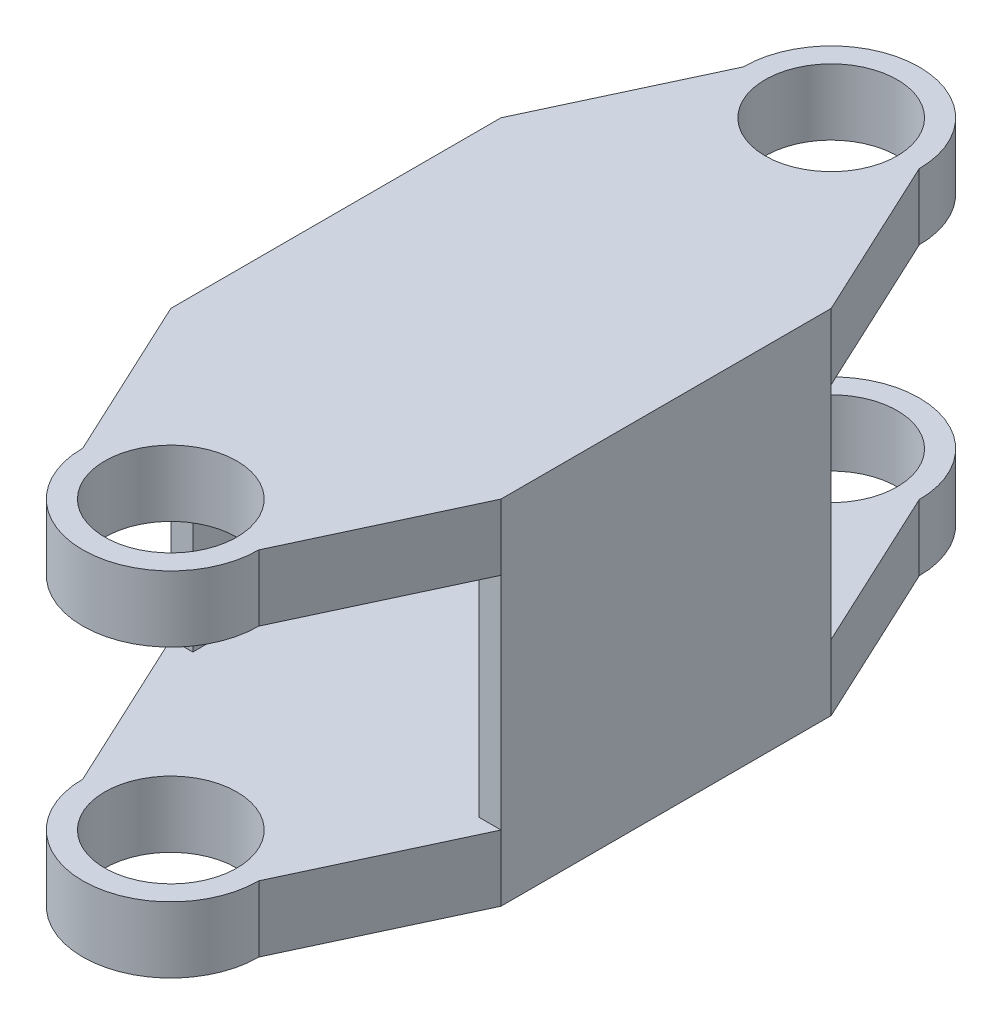
SolidWorks part; units mm, degrees
ref_plane "Plano frontal" through (0, 0, 0) normal (0, 0, 1) x (1, 0, 0)
ref_plane "Plano superior" through (0, 0, 0) normal (0, 1, 0) x (1, 0, 0)
ref_plane "Plano direito" through (0, 0, 0) normal (1, 0, 0) x (0, 0, -1)
ref_plane "Plane1" through (0, 5.01, 0) normal (0, 1, 0) x (1, 0, 0)
sketch "Sketch1" plane through (0, 5.01, 0) normal (0, 1, 0) x (1, 0, 0)
  line L0 (0, 19) -> (0, -11.6822) construction
  line L1 (14.8327, 0) -> (-20.4647, 0) construction
  line L2 (22.7509, 7.5) -> (-22.4164, 7.5) construction
  line L4 (-7.5, -7.5) -> (-7.5, 7.5)
  line L6 (7.5, -7.5) -> (7.5, 7.5)
  line L7 (-7.5, -7.5) -> (7.5, 7.5) construction
  line L8 (-7.5, 7.5) -> (7.5, -7.5) construction
  line L9 (-4, 15) -> (4, 15) construction
  line L10 (-4, 15) -> (-7.5, 7.5)
  line L11 (4, 15) -> (7.5, 7.5)
  line L12 (4, -15) -> (7.5, -7.5)
  line L13 (-4, -15) -> (-7.5, -7.5)
  arc A0 (-4, 15) -> (4, 15) centre (0, 15) cw
  circle A1 centre (0, 15) radius 3
  circle A2 centre (0, -15) radius 3
  arc A3 (-4, -15) -> (4, -15) centre (0, -15) ccw
  point P5 (0, 0)
  dimension "D5" = 6
  dimension "D1" = 15
  dimension "D2" = 8
  dimension "D3" = 4
  dimension "D4" = 7.5
extrude "Boss-Extrude1" add sketch "Sketch1" along normal blind 3
sketch "Sketch4" plane through (0, 5.01, 0) normal (0, 1, 0) x (1, 0, 0)
  line L0 (7.5, 7.5) -> (7.5, -7.5)
  line L1 (7.5, 7.5) -> (6.5, 7.5)
  line L2 (7.5, -7.5) -> (6.5, -7.5)
  line L3 (6.5, 7.5) -> (6.5, -7.5)
  dimension "D1" = 1
sketch "Sketch5" plane through (0, 0, 0) normal (0, 1, 0) x (1, 0, 0)
  line L0 (7.5, 7.5) -> (7.5, -7.5)
  line L1 (7.5, 7.5) -> (6.5, 7.5)
  line L2 (7.5, -7.5) -> (6.5, -7.5)
  line L3 (6.5, 7.5) -> (6.5, -7.5)
  dimension "D1" = 1
loft "Loft2" add profiles "Sketch5", "Sketch4"
sketch "Sketch6" plane through (0, 5.01, 0) normal (0, 1, 0) x (1, 0, 0)
  line L0 (-7.5, 7.5) -> (-7.5, -7.5)
  line L1 (-7.5, 7.5) -> (-6.5, 7.5)
  line L2 (-7.5, -7.5) -> (-6.5, -7.5)
  line L3 (-6.5, 7.5) -> (-6.5, -7.5)
  dimension "D1" = 1
sketch "Sketch7" plane through (0, 0, 0) normal (0, 1, 0) x (1, 0, 0)
  line L0 (-7.5, 7.5) -> (-7.5, -7.5)
  line L1 (-7.5, 7.5) -> (-6.5, 7.5)
  line L2 (-7.5, -7.5) -> (-6.5, -7.5)
  line L3 (-6.5, 7.5) -> (-6.5, -7.5)
  dimension "D1" = 1
loft "Loft3" add profiles "Sketch7", "Sketch6"
mirror "Mirror2" about plane through (0, 0, 0) normal (0, 1, 0) of "Boss-Extrude1", "Loft2", "Loft3"
